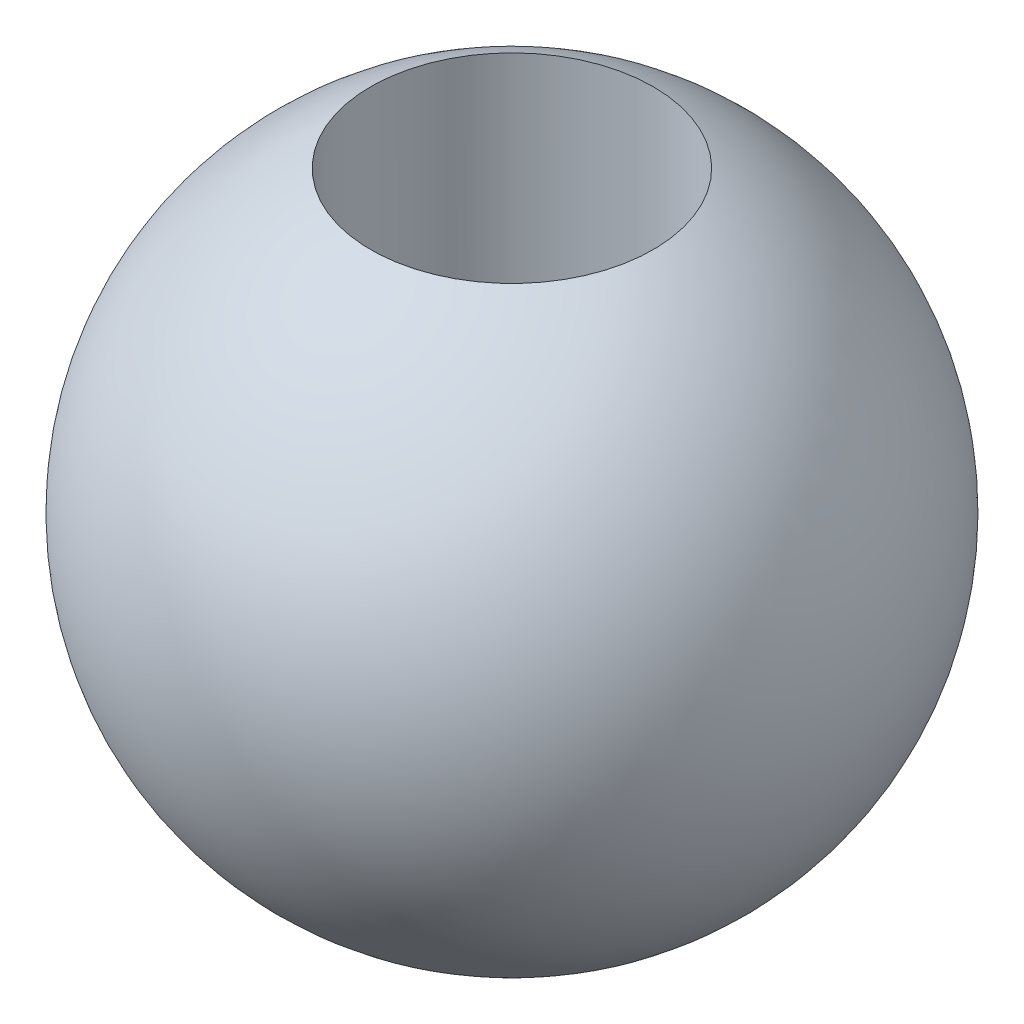
SolidWorks part; units mm, degrees
material "Cast Alloy Steel"
ref_plane "Front Plane" through (0, 0, 0) normal (0, 0, 1) x (1, 0, 0)
ref_plane "Top Plane" through (0, 0, 0) normal (0, 1, 0) x (1, 0, 0)
ref_plane "Right Plane" through (0, 0, 0) normal (1, 0, 0) x (0, 0, -1)
sketch "Sketch1" plane through (0, 0, 0) normal (0, 0, 1) x (1, 0, 0)
  line L0 (0, -7) -> (0, 7)
  arc A0 (0, 7) -> (0, -7) centre (0, 0) cw
  point P4 (0, 0)
  dimension "D1" = 14
revolve "Revolve1" add sketch "Sketch1" angle 360 about L0
sketch "Sketch2" plane through (0, 0, 0) normal (0, 1, 0) x (1, 0, 0)
  circle A0 centre (0, 0) radius 3
  dimension "D1" = 6
extrude "Cut-Extrude1" cut sketch "Sketch2" against normal through all both and the other way through all
